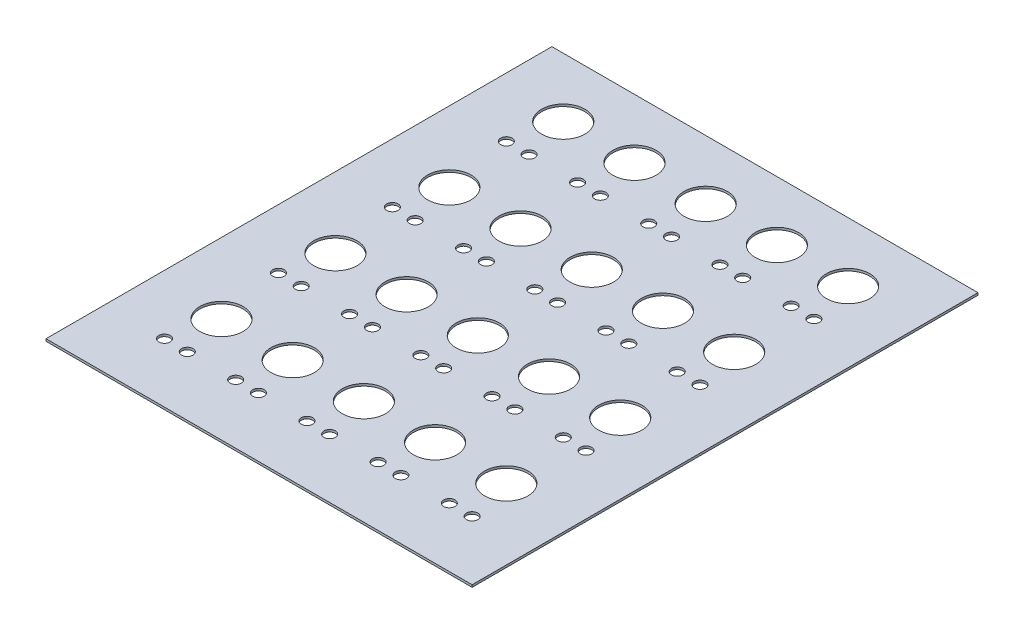
SolidWorks part; units mm, degrees
ref_plane "Front Plane" through (0, 0, 0) normal (0, 0, 1) x (1, 0, 0)
ref_plane "Top Plane" through (0, 0, 0) normal (0, 1, 0) x (1, 0, 0)
ref_plane "Right Plane" through (0, 0, 0) normal (1, 0, 0) x (0, 0, -1)
sketch "Sketch1" plane through (0, 0, 0) normal (0, 1, 0) x (1, 0, 0)
  line L1 (-29.0374, 147.0182) -> (157.9626, 147.0182)
  line L2 (-29.0374, 147.0182) -> (-29.0374, -74.9818)
  line L3 (-29.0374, -74.9818) -> (157.9626, -74.9818)
  line L4 (157.9626, 147.0182) -> (157.9626, -74.9818)
  circle A0 centre (-3.0374, -48.9818) radius 2.5
  circle A1 centre (6.9626, -48.9818) radius 2.5
  circle A2 centre (28.2126, -48.9818) radius 2.5
  circle A3 centre (38.2126, -48.9818) radius 2.5
  circle A4 centre (1.9626, -28.9818) radius 9.5
  circle A5 centre (33.2126, -28.9818) radius 9.5
  circle A6 centre (59.4626, -48.9818) radius 2.5
  circle A7 centre (69.4626, -48.9818) radius 2.5
  circle A8 centre (64.4626, -28.9818) radius 9.5
  circle A9 centre (90.7126, -48.9818) radius 2.5
  circle A10 centre (100.7126, -48.9818) radius 2.5
  circle A11 centre (95.7126, -28.9818) radius 9.5
  circle A12 centre (121.9626, -48.9818) radius 2.5
  circle A13 centre (131.9626, -48.9818) radius 2.5
  circle A14 centre (126.9626, -28.9818) radius 9.5
  circle A15 centre (-3.0374, 1.0182) radius 2.5
  circle A16 centre (6.9626, 1.0182) radius 2.5
  circle A17 centre (1.9626, 21.0182) radius 9.5
  circle A18 centre (28.2126, 1.0182) radius 2.5
  circle A19 centre (38.2126, 1.0182) radius 2.5
  circle A20 centre (33.2126, 21.0182) radius 9.5
  circle A21 centre (59.4626, 1.0182) radius 2.5
  circle A22 centre (69.4626, 1.0182) radius 2.5
  circle A23 centre (64.4626, 21.0182) radius 9.5
  circle A24 centre (90.7126, 1.0182) radius 2.5
  circle A25 centre (100.7126, 1.0182) radius 2.5
  circle A26 centre (95.7126, 21.0182) radius 9.5
  circle A27 centre (121.9626, 1.0182) radius 2.5
  circle A28 centre (131.9626, 1.0182) radius 2.5
  circle A29 centre (126.9626, 21.0182) radius 9.5
  circle A30 centre (-3.0374, 51.0182) radius 2.5
  circle A31 centre (6.9626, 51.0182) radius 2.5
  circle A32 centre (1.9626, 71.0182) radius 9.5
  circle A33 centre (28.2126, 51.0182) radius 2.5
  circle A34 centre (38.2126, 51.0182) radius 2.5
  circle A35 centre (33.2126, 71.0182) radius 9.5
  circle A36 centre (59.4626, 51.0182) radius 2.5
  circle A37 centre (69.4626, 51.0182) radius 2.5
  circle A38 centre (64.4626, 71.0182) radius 9.5
  circle A39 centre (90.7126, 51.0182) radius 2.5
  circle A40 centre (100.7126, 51.0182) radius 2.5
  circle A41 centre (95.7126, 71.0182) radius 9.5
  circle A42 centre (121.9626, 51.0182) radius 2.5
  circle A43 centre (131.9626, 51.0182) radius 2.5
  circle A44 centre (126.9626, 71.0182) radius 9.5
  circle A45 centre (-3.0374, 101.0182) radius 2.5
  circle A46 centre (6.9626, 101.0182) radius 2.5
  circle A47 centre (1.9626, 121.0182) radius 9.5
  circle A48 centre (28.2126, 101.0182) radius 2.5
  circle A49 centre (38.2126, 101.0182) radius 2.5
  circle A50 centre (33.2126, 121.0182) radius 9.5
  circle A51 centre (59.4626, 101.0182) radius 2.5
  circle A52 centre (69.4626, 101.0182) radius 2.5
  circle A53 centre (64.4626, 121.0182) radius 9.5
  circle A54 centre (90.7126, 101.0182) radius 2.5
  circle A55 centre (100.7126, 101.0182) radius 2.5
  circle A56 centre (95.7126, 121.0182) radius 9.5
  circle A57 centre (121.9626, 101.0182) radius 2.5
  circle A58 centre (131.9626, 101.0182) radius 2.5
  circle A59 centre (126.9626, 121.0182) radius 9.5
  point P8 (0, 0)
  dimension "D3" = 5
  dimension "D6" = 19
  dimension "D9" = 10
  dimension "D11" = 31
  dimension "D12" = 26
  dimension "D13" = 26
  dimension "D14" = 31
  dimension "D1" = 222
  dimension "D2" = 156
  dimension "D4" = 20
  dimension "D5" = 5
  dimension "D7" = 20
  dimension "D8" = 4
  dimension "D10" = 5
  dimension "D15" = 187
extrude "Boss-Extrude1" add sketch "Sketch1" along normal blind 1
